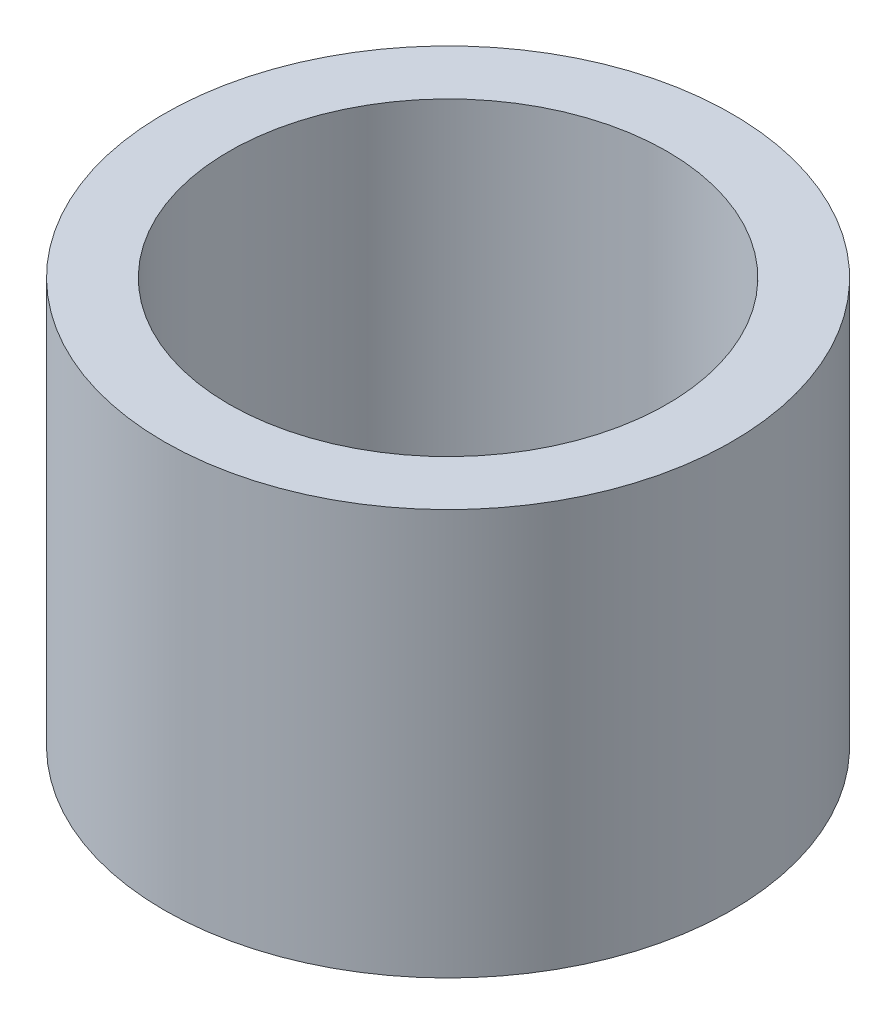
SolidWorks part; units mm, degrees
ref_plane "Front Plane" through (0, 0, 0) normal (0, 0, 1) x (1, 0, 0)
ref_plane "Top Plane" through (0, 0, 0) normal (0, 1, 0) x (1, 0, 0)
ref_plane "Right Plane" through (0, 0, 0) normal (1, 0, 0) x (0, 0, -1)
sketch "Sketch2" plane through (0, 0, 0) normal (0, 1, 0) x (1, 0, 0)
  circle A0 centre (0, 0) radius 3.5
  circle A1 centre (0, 0) radius 2.7
  dimension "D1" = 7
  dimension "D2" = 5.4
extrude "Boss-Extrude1" add sketch "Sketch2" along normal blind 5
